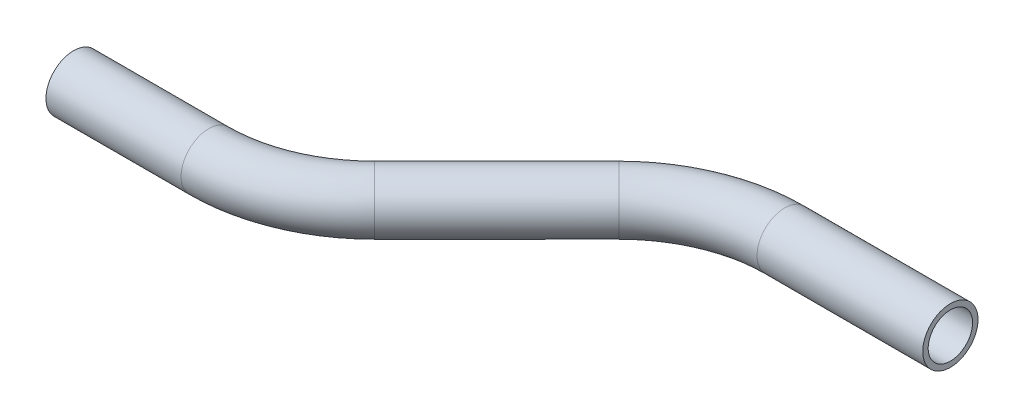
SolidWorks part; units mm, degrees
material "AISI Type 316L stainless steel"
ref_plane "Front Plane" through (0, 0, 0) normal (0, 0, 1) x (1, 0, 0)
ref_plane "Top Plane" through (0, 0, 0) normal (0, 1, 0) x (1, 0, 0)
ref_plane "Right Plane" through (0, 0, 0) normal (1, 0, 0) x (0, 0, -1)
sketch "Sketch1" plane through (0, 0, 0) normal (0, 1, 0) x (1, 0, 0)
  line L0 (0, 0) -> (31.0664, 0)
  line L1 (58.0071, 11.1592) -> (86.1048, 39.2569)
  line L2 (113.0456, 50.4161) -> (151.1456, 50.4161)
  arc A1 (86.1048, 39.2569) -> (113.0456, 50.4161) centre (113.0456, 12.3161) cw
  arc A2 (31.0664, 0) -> (58.0071, 11.1592) centre (31.0664, 38.1) ccw
  point P10 (97.264, 50.4161)
  point P14 (46.8479, 0)
  dimension "D3" = 38.1
  dimension "D1" = 151.1456
  dimension "D2" = 38.1
  dimension "D4" = 45
  dimension "D5" = 50.4161
ref_plane "Plane1" through (0, 0, 0) normal (1, 0, 0) x (0, 0, -1)
sketch "Sketch2" plane through (0, 0, 0) normal (1, 0, 0) x (0, 0, -1)
  circle A0 centre (0, 0) radius 6.35
  circle A1 centre (0, 0) radius 5.1054
  dimension "D1" = 12.7
  dimension "D2" = 1.2446
sweep "Sweep1" add profiles "Sketch2" path "Sketch1"
